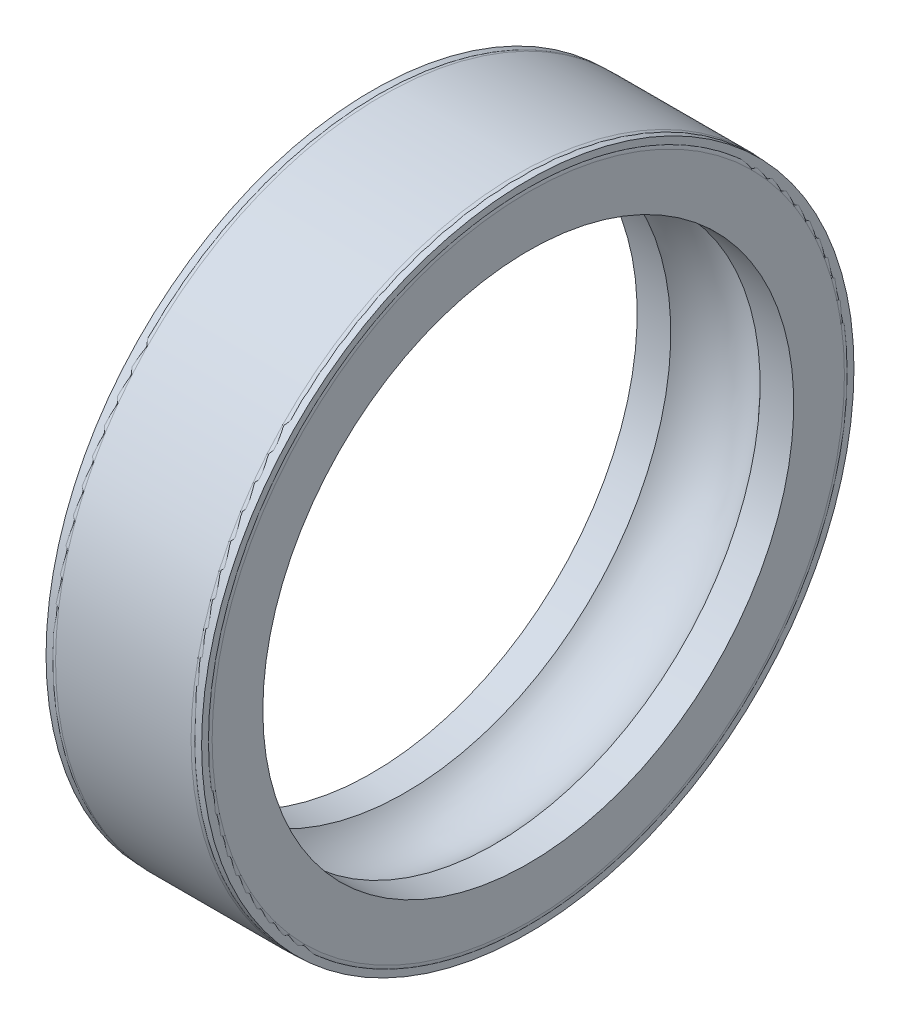
SolidWorks part; units mm, degrees
ref_plane "Front Plane" through (0, 0, 0) normal (0, 0, 1) x (1, 0, 0)
ref_plane "Top Plane" through (0, 0, 0) normal (0, 1, 0) x (1, 0, 0)
ref_plane "Right Plane" through (0, 0, 0) normal (1, 0, 0) x (0, 0, -1)
sketch "Sketch1" plane through (0, 0, 0) normal (0, 1, 0) x (1, 0, 0)
  line L0 (-398.6226, -2.832) -> (388.7774, -2.832)
  line L1 (0, 1343.368) -> (0, 0) construction
  line L6 (0, 1343.368) -> (0, 1479.3414)
  line L7 (-393.7, 1648.168) -> (393.7, 1648.168)
  line L8 (-393.7, 1648.168) -> (-393.7, 1343.368)
  line L10 (393.7, 1648.168) -> (393.7, 1343.368)
  line L11 (-393.7, 1648.168) -> (393.7, 1343.368) construction
  line L12 (-393.7, 1343.368) -> (393.7, 1648.168) construction
  line L15 (-393.7, 1343.368) -> (-227.1845, 1343.368)
  line L16 (227.1845, 1343.368) -> (393.7, 1343.368)
  arc A0 (-227.1845, 1343.368) -> (227.1845, 1343.368) centre (0, 1140.168) cw
  point P10 (0, 1495.768)
  dimension "D5" = 304.8
  dimension "D1" = 1651
  dimension "D3" = 787.4
  dimension "D4" = 203.2
revolve "Revolve-Thin1" add sketch "Sketch1" angle 360 about L0
fillet "Fillet5" radius 53.34 2 edges at (-396.24, 0, 1656.372) (396.24, 0, 1656.372)
